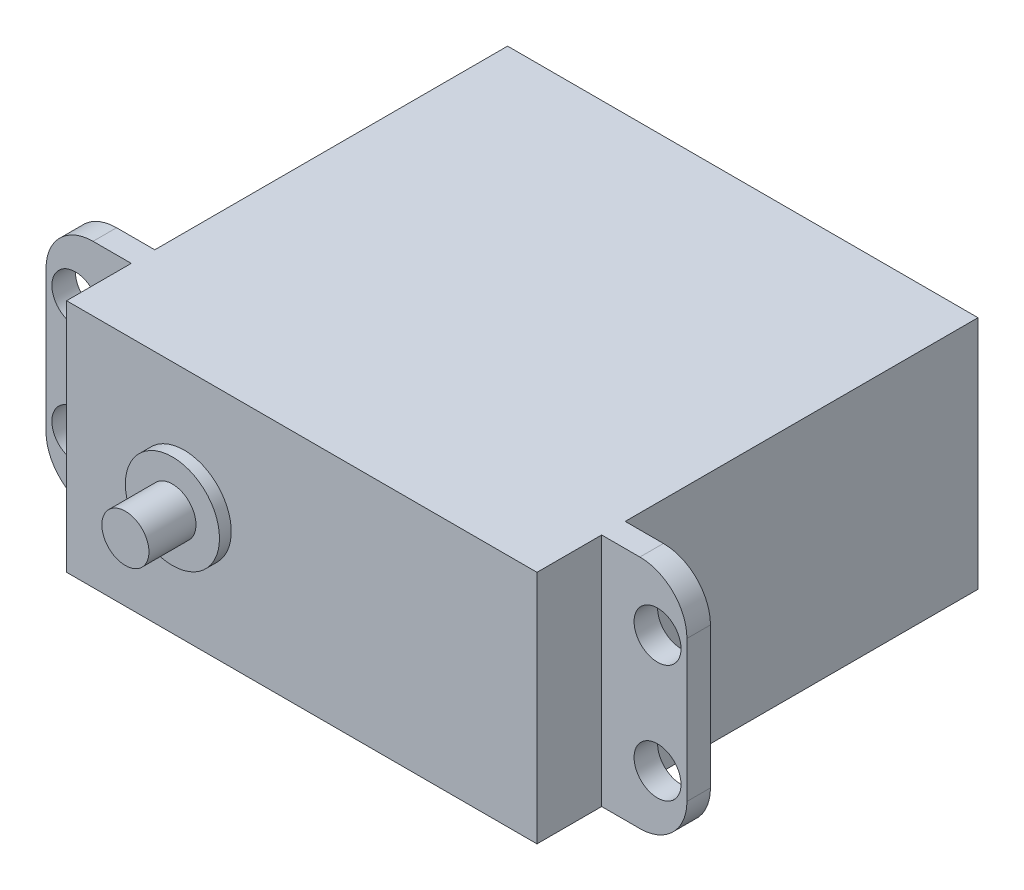
SolidWorks part; units mm, degrees
ref_plane "Front Plane" through (0, 0, 0) normal (0, 0, 1) x (1, 0, 0)
ref_plane "Top Plane" through (0, 0, 0) normal (0, 1, 0) x (1, 0, 0)
ref_plane "Right Plane" through (0, 0, 0) normal (1, 0, 0) x (0, 0, -1)
sketch "Sketch1" plane through (0, 0, 0) normal (0, 0, 1) x (1, 0, 0)
  line L1 (-20, -10) -> (20, -10)
  line L2 (-20, -10) -> (-20, 10)
  line L3 (-20, 10) -> (20, 10)
  line L4 (20, -10) -> (20, 10)
  line L5 (-20, -10) -> (20, 10) construction
  line L6 (-20, 10) -> (20, -10) construction
  point P0 (0, 0)
  point P6 (0, 0)
extrude "Boss-Extrude2" add sketch "Sketch1" along normal blind 37.5 contours L3 L4 L1 L2
sketch "Sketch2" plane through (20, 0, 0) normal (1, 0, 0) x (0, 0, -1)
  line L0 (-37.5, -10) -> (-32, -10)
  line L1 (-37.5, -10) -> (0, -10) construction
  line L2 (-32, -10) -> (-32, 10)
  line L3 (-37.5, 10) -> (0, 10) construction
  line L4 (-32, 10) -> (-30, 10)
  line L5 (-30, 10) -> (-30, -10)
  line L6 (-30, -10) -> (-32, -10)
  point P5 (0, 0)
  point P11 (0, 0)
extrude "Boss-Extrude3" add sketch "Sketch2" along normal blind 7.25 contours L2 L4 L5 L6
sketch "Sketch3" plane through (0, 0, 32) normal (0, 0, 1) x (1, 0, 0)
  circle A0 centre (24.75, -4.9991) radius 1.9955
  circle A1 centre (24.75, 4.9994) radius 1.9955
extrude "Cut-Extrude1" cut sketch "Sketch3" against normal blind 2 contours A1 | A0
fillet "Fillet3" radius 4 2 edges at (27.25, 10, 31) (27.25, -10, 31)
sketch "Sketch4" plane through (-20, 0, 0) normal (-1, 0, 0) x (0, 0, 1)
  line L0 (37.5, -10) -> (32, -10)
  line L1 (37.5, -10) -> (0, -10) construction
  line L2 (32, -10) -> (32, 10)
  line L3 (37.5, 10) -> (0, 10) construction
  line L4 (32, 10) -> (30, 10)
  line L5 (30, 10) -> (30, -10)
  line L6 (30, -10) -> (32, -10)
  point P5 (0, 0)
  point P11 (0, 0)
extrude "Boss-Extrude4" add sketch "Sketch4" along normal blind 7.25 contours L2 L4 L5 L6
sketch "Sketch5" plane through (0, 0, 32) normal (0, 0, 1) x (1, 0, 0)
  circle A0 centre (-24.75, 5) radius 2
  circle A1 centre (-24.75, -5) radius 2
extrude "Cut-Extrude2" cut sketch "Sketch5" against normal blind 2
fillet "Fillet4" radius 4 2 edges at (-27.25, -10, 31) (-27.25, 10, 31)
sketch "Sketch6" plane through (0, 0, 37.5) normal (0, 0, 1) x (1, 0, 0)
  circle A1 centre (-10, 0) radius 4.0013
extrude "Boss-Extrude5" add sketch "Sketch6" along normal blind 1
sketch "Sketch7" plane through (0, 0, 38.5) normal (0, 0, 1) x (1, 0, 0)
  circle A0 centre (-10, 0) radius 2.0015
  point P3 (-32.5114, 8.2782)
extrude "Boss-Extrude7" add sketch "Sketch7" along normal blind 4
